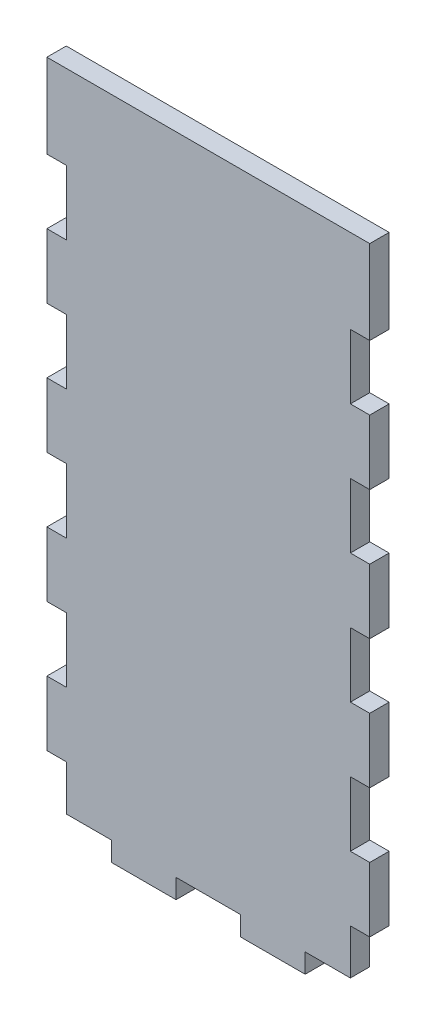
SolidWorks part; units mm, degrees
ref_plane "Front Plane" through (0, 0, 0) normal (0, 0, 1) x (1, 0, 0)
ref_plane "Top Plane" through (0, 0, 0) normal (0, 1, 0) x (1, 0, 0)
ref_plane "Right Plane" through (0, 0, 0) normal (1, 0, 0) x (0, 0, -1)
sketch "Sketch1" plane through (0, 0, 0) normal (0, 0, 1) x (1, 0, 0)
  line L1 (-10, 199.4274) -> (90, 199.4274)
  line L2 (-10, 199.4274) -> (-10, -6.5726)
  line L3 (-10, -6.5726) -> (90, -6.5726)
  line L4 (90, 199.4274) -> (90, -6.5726)
  dimension "D1" = 100
  dimension "D2" = 206
extrude "Boss-Extrude1" add sketch "Sketch1" along normal blind 6
sketch "Sketch2" plane through (0, 0, 0) normal (0, 0, 1) x (1, 0, 0)
  line L0 (-10, 199.4274) -> (-10, -6.5726) construction
  line L1 (-10, -6.5726) -> (-4, -6.5726)
  line L2 (-10, -6.5726) -> (-10, 13.4274)
  line L3 (-10, 13.4274) -> (-4, 13.4274)
  line L4 (-4, -6.5726) -> (-4, 13.4274)
  line L5 (-10, -6.5726) -> (90, -6.5726) construction
  dimension "D1" = 20
  dimension "D2" = 0
  dimension "D3" = 6
extrude "Cut-Extrude1" cut sketch "Sketch2" along normal blind 10
pattern_linear "LPattern1" count 5 spacing 40 along (0, 1, 0) of "Cut-Extrude1"
sketch "Sketch3" plane through (0, 0, 6) normal (0, 0, 1) x (1, 0, 0)
  line L0 (40, 199.4274) -> (40, -6.5726)
  line L1 (90, 199.4274) -> (-10, 199.4274) construction
  line L2 (-4, -6.5726) -> (90, -6.5726) construction
ref_plane "Plane1" through (40, 0, 0) normal (1, 0, 0) x (0, 0, -1)
mirror "Mirror2" about plane through (40, 0, 0) normal (1, 0, 0) of "LPattern1", "Cut-Extrude1"
sketch "Sketch4" plane through (0, 0, 6) normal (0, 0, 1) x (1, 0, 0)
  line L0 (-4, -6.5726) -> (84, -6.5726) construction
  line L1 (-10, -6.5726) -> (10, -6.5726)
  line L2 (-10, -6.5726) -> (-10, -0.5726)
  line L3 (-10, -0.5726) -> (10, -0.5726)
  line L4 (10, -6.5726) -> (10, -0.5726)
  line L5 (-10, 33.4274) -> (-10, 13.4274) construction
  dimension "D1" = 0
  dimension "D2" = 6
  dimension "D3" = 20
extrude "Cut-Extrude2" cut sketch "Sketch4" against normal blind 10
pattern_linear "LPattern2" count 3 spacing 40 along (1, 0, 0) of "Cut-Extrude2"
